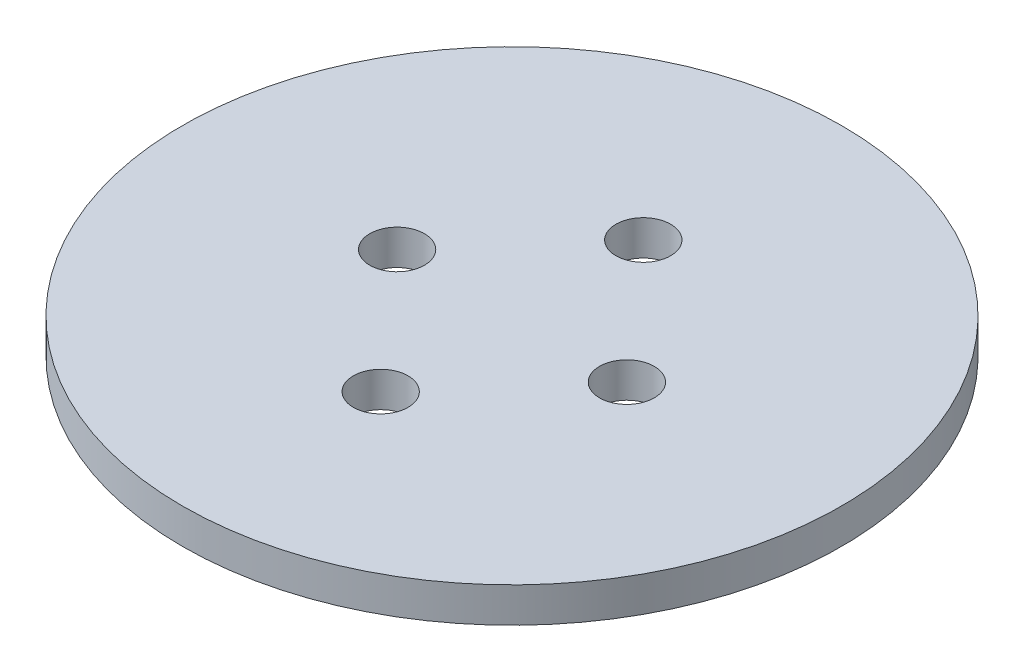
SolidWorks part; units mm, degrees
material "Pine"
ref_plane "Front Plane" through (0, 0, 0) normal (0, 0, 1) x (1, 0, 0)
ref_plane "Top Plane" through (0, 0, 0) normal (0, 1, 0) x (1, 0, 0)
ref_plane "Right Plane" through (0, 0, 0) normal (1, 0, 0) x (0, 0, -1)
sketch "Sketch1" plane through (0, 0, 0) normal (0, 1, 0) x (1, 0, 0)
  circle A0 centre (0, 0) radius 47.8155
  dimension "D1" = 95.631
extrude "Boss-Extrude1" add sketch "Sketch1" along normal blind 5.08
hole_wizard "U-bolt Holes" positions "Sketch2" profile "Sketch3" tap size "5/16-18" standard "ANSI Inch" end condition through all
sketch "Sketch2" plane through (0, 5.08, 0) normal (0, 1, 0) x (1, 0, 0)
  line L0 (0, 0) -> (0, 20.4425) construction
  point P0 (-16.6687, 0)
  point P12 (16.6687, 0)
  dimension "D1" = 33.3375
sketch "Sketch3" plane through (-16.6687, 5.08, 0) normal (1, 0, 0) x (0, 0, 1)
  line L0 (0, 0) -> (0, 5.08)
  line L1 (0, 5.08) -> (3.9687, 5.08)
  line L2 (3.9687, 5.08) -> (3.9687, 0)
  line L5 (3.9687, 0) -> (0, 0)
  line L11 (0, -6.35) -> (0, 107.95) construction
  dimension "Thru Tap Drill Dia." = 7.9375
  dimension "Thru Tap Drill Depth" = 5.08
cosmetic thread "Hole Thread1"
cosmetic thread "Hole Thread2"
hole_wizard "Threaded Rod Holes" positions "Sketch4" profile "Sketch5" tap size "5/16-18" standard "ANSI Inch" end condition through all
sketch "Sketch4" plane through (0, 5.08, 0) normal (0, 1, 0) x (1, 0, 0)
  line L1 (0, 0) -> (0, -19.05) construction
  line L3 (0, 0) -> (0, 19.05) construction
  point P13 (0, -19.05)
  point P17 (0, 19.05)
  dimension "D1" = 38.1
sketch "Sketch5" plane through (0, 5.08, -19.05) normal (1, 0, 0) x (0, 0, 1)
  line L0 (0, 0) -> (0, 5.08)
  line L1 (0, 5.08) -> (3.9687, 5.08)
  line L2 (3.9687, 5.08) -> (3.9687, 0)
  line L5 (3.9687, 0) -> (0, 0)
  line L11 (0, -6.35) -> (0, 107.95) construction
  dimension "Thru Tap Drill Dia." = 7.9375
  dimension "Thru Tap Drill Depth" = 5.08
cosmetic thread "Hole Thread3"
cosmetic thread "Hole Thread4"
